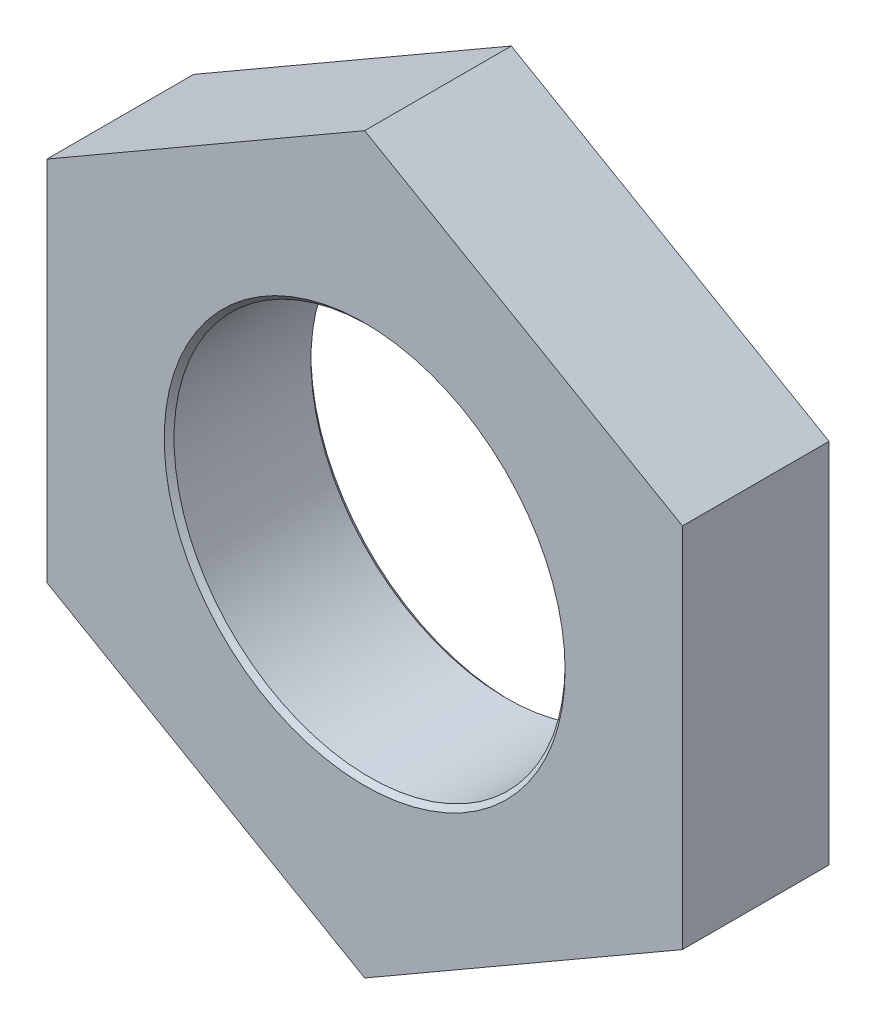
SolidWorks part; units mm, degrees
ref_plane "前视基准面" through (0, 0, 0) normal (0, 0, 1) x (1, 0, 0)
ref_plane "上视基准面" through (0, 0, 0) normal (0, 1, 0) x (1, 0, 0)
ref_plane "右视基准面" through (0, 0, 0) normal (1, 0, 0) x (0, 0, -1)
sketch "草图1" plane through (0, 0, 0) normal (0, 0, 1) x (1, 0, 0)
  line L1 (0, 7.5056) -> (-6.5, 3.7528)
  line L2 (-6.5, 3.7528) -> (-6.5, -3.7528)
  line L3 (-6.5, -3.7528) -> (0, -7.5056)
  line L4 (0, -7.5056) -> (6.5, -3.7528)
  line L5 (6.5, -3.7528) -> (6.5, 3.7528)
  line L6 (6.5, 3.7528) -> (0, 7.5056)
  circle A0 centre (0, 0) radius 6.5 construction
  dimension "D1" = 13
extrude "凸台-拉伸1" add sketch "草图1" against normal blind 3
sketch "草图2" plane through (0, 0, 0) normal (0, 0, 1) x (1, 0, 0)
  circle A0 centre (0, 0) radius 4
extrude "切除-拉伸1" cut sketch "草图2" against normal blind 3
cosmetic thread "装饰螺纹线1"
chamfer "倒角1" distance 0.1 angle 45 2 edges at (4, 0, 0) (4, 0, -3)
